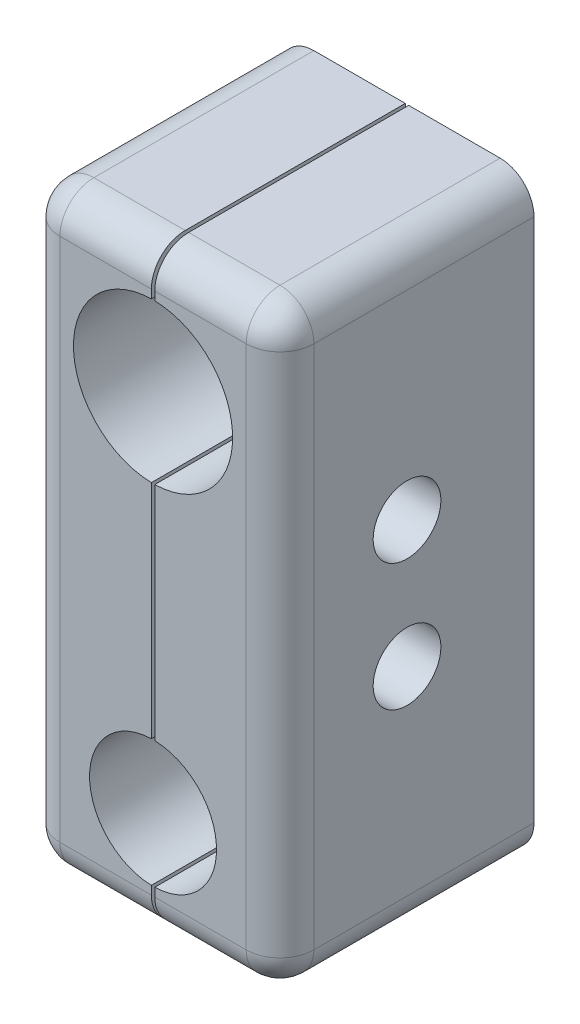
SolidWorks part; units mm, degrees
ref_plane "Front Plane" through (0, 0, 0) normal (0, 0, 1) x (1, 0, 0)
ref_plane "Top Plane" through (0, 0, 0) normal (0, 1, 0) x (1, 0, 0)
ref_plane "Right Plane" through (0, 0, 0) normal (1, 0, 0) x (0, 0, -1)
sketch "Sketch1" plane through (0, 0, 0) normal (0, 0, 1) x (1, 0, 0)
  line L1 (9.525, 22.225) -> (-9.525, 22.225)
  line L2 (9.525, 22.225) -> (9.525, -22.225)
  line L3 (9.525, -22.225) -> (-9.525, -22.225)
  line L4 (-9.525, 22.225) -> (-9.525, -22.225)
  line L5 (9.525, 22.225) -> (-9.525, -22.225) construction
  line L6 (9.525, -22.225) -> (-9.525, 22.225) construction
  point P0 (0, 0)
  dimension "D1" = 19.05
  dimension "D2" = 44.45
extrude "Boss-Extrude1" add sketch "Sketch1" along normal blind 19.05
sketch "Sketch2" plane through (0, 0, 19.05) normal (0, 0, 1) x (1, 0, 0)
  line L0 (9.525, 22.225) -> (-9.525, 22.225) construction
  line L1 (-9.525, -22.225) -> (9.525, -22.225) construction
  line L2 (0, -14.2875) -> (0, 13.081) construction
  circle A0 centre (0, 13.081) radius 5.969
  circle A1 centre (0, -14.2875) radius 4.7625
  point P4 (0, -19.05)
  point P5 (0, 19.05)
  point P10 (-0.5464, 11.817)
  dimension "D1" = 3.175
  dimension "D3" = 9.525
  dimension "D4" = 11.938
  dimension "D2" = 3.175
extrude "Cut-Extrude1" cut sketch "Sketch2" against normal up to next
sketch "Sketch3" plane through (9.525, 0, 0) normal (1, 0, 0) x (0, 0, -1)
  line L0 (-9.525, -4.7625) -> (-9.525, 4.7625) construction
  line L1 (-9.525, 0) -> (0, 0) construction
  line L2 (0, -22.225) -> (0, 22.225) construction
  line L3 (-9.525, 0) -> (-19.05, 0) construction
  line L4 (-19.05, -22.225) -> (-19.05, 22.225) construction
  circle A0 centre (-9.525, -4.7625) radius 1.5875
  circle A1 centre (-9.525, 4.7625) radius 1.5875
  dimension "D1" = 9.525
  dimension "D2" = 3.175
extrude "Cut-Extrude2" cut sketch "Sketch3" against normal up to next
sketch "Sketch6" plane through (9.525, 0, 0) normal (1, 0, 0) x (0, 0, -1)
  circle A0 centre (-9.525, -4.7625) radius 2.54
  circle A1 centre (-9.525, 4.7625) radius 2.54
  dimension "D1" = 5.08
extrude "Cut-Extrude5" cut sketch "Sketch6" against normal blind 3.81
sketch "Sketch4" plane through (-9.525, 0, 0) normal (-1, 0, 0) x (0, 0, 1)
  line L1 (9.525, 1.023) -> (12.7635, 2.8928)
  line L2 (12.7635, 2.8928) -> (12.7635, 6.6322)
  line L3 (12.7635, 6.6322) -> (9.525, 8.502)
  line L4 (9.525, 8.502) -> (6.2865, 6.6322)
  line L5 (6.2865, 6.6322) -> (6.2865, 2.8928)
  line L6 (6.2865, 2.8928) -> (9.525, 1.023)
  line L7 (9.525, -8.502) -> (12.7635, -6.6322)
  line L8 (12.7635, -6.6322) -> (12.7635, -2.8928)
  line L9 (12.7635, -2.8928) -> (9.525, -1.023)
  line L10 (9.525, -1.023) -> (6.2865, -2.8928)
  line L11 (6.2865, -2.8928) -> (6.2865, -6.6322)
  line L12 (6.2865, -6.6322) -> (9.525, -8.502)
  circle A0 centre (9.525, 4.7625) radius 3.2385 construction
  circle A1 centre (9.525, -4.7625) radius 3.2385 construction
  point P10 (5.7855, -4.7625)
  point P19 (5.7855, -4.7625)
  dimension "D1" = 6.477
extrude "Cut-Extrude3" cut sketch "Sketch4" against normal blind 3.9688
fillet "Fillet1" radius 2.54 8 edges at (0, 22.225, 19.05) (-9.525, 0, 19.05) (9.525, 0, 19.05) (0, -22.225, 19.05) (-9.525, 22.225, 9.525) (9.525, 22.225, 9.525) (9.525, -22.225, 9.525) (-9.525, -22.225, 9.525)
sketch "Sketch5" plane through (0, 0, 0) normal (0, 0, -1) x (-1, 0, 0)
  line L0 (-6.985, 22.225) -> (6.985, 22.225) construction
  line L1 (-0.127, -22.225) -> (0.127, -22.225)
  line L2 (-0.127, -22.225) -> (-0.127, 22.225)
  line L3 (-0.127, 22.225) -> (0.127, 22.225)
  line L4 (0.127, -22.225) -> (0.127, 22.225)
  line L5 (-0.127, -22.225) -> (0.127, 22.225) construction
  line L6 (-0.127, 22.225) -> (0.127, -22.225) construction
  point P0 (0, 0)
  point P5 (0, 0)
  point P9 (0, 0)
  dimension "D1" = 0.254
extrude "Cut-Extrude4" cut sketch "Sketch5" against normal up to next
